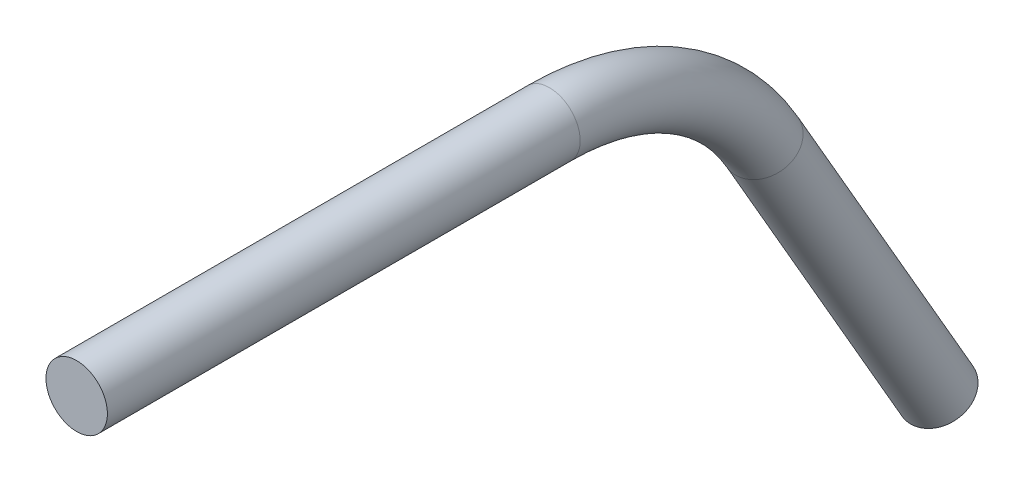
SolidWorks part; units mm, degrees
ref_plane "Front Plane" through (0, 0, 0) normal (0, 0, 1) x (1, 0, 0)
ref_plane "Top Plane" through (0, 0, 0) normal (0, 1, 0) x (1, 0, 0)
ref_plane "Right Plane" through (0, 0, 0) normal (1, 0, 0) x (0, 0, -1)
sketch "Sketch2" plane through (0, 0, 0) normal (0, 0, 1) x (1, 0, 0)
  circle A0 centre (0, 0) radius 3.175
  dimension "D1" = 6.35
sketch "Sketch4" plane through (0, 0, 0) normal (1, 0, 0) x (0, 0, -1)
  line L0 (0, 0) -> (48.8353, 0)
  line L1 (70.8323, -12.7) -> (88.9, -43.9941)
  arc A0 (70.8323, -12.7) -> (48.8353, 0) centre (48.8353, -25.4) ccw
  point P6 (63.5, 0)
  dimension "D4" = 25.4
  dimension "D1" = 63.5
  dimension "D2" = 50.8
  dimension "D3" = 60
sweep "Sweep1" add profiles "Sketch2" path "Sketch4"
